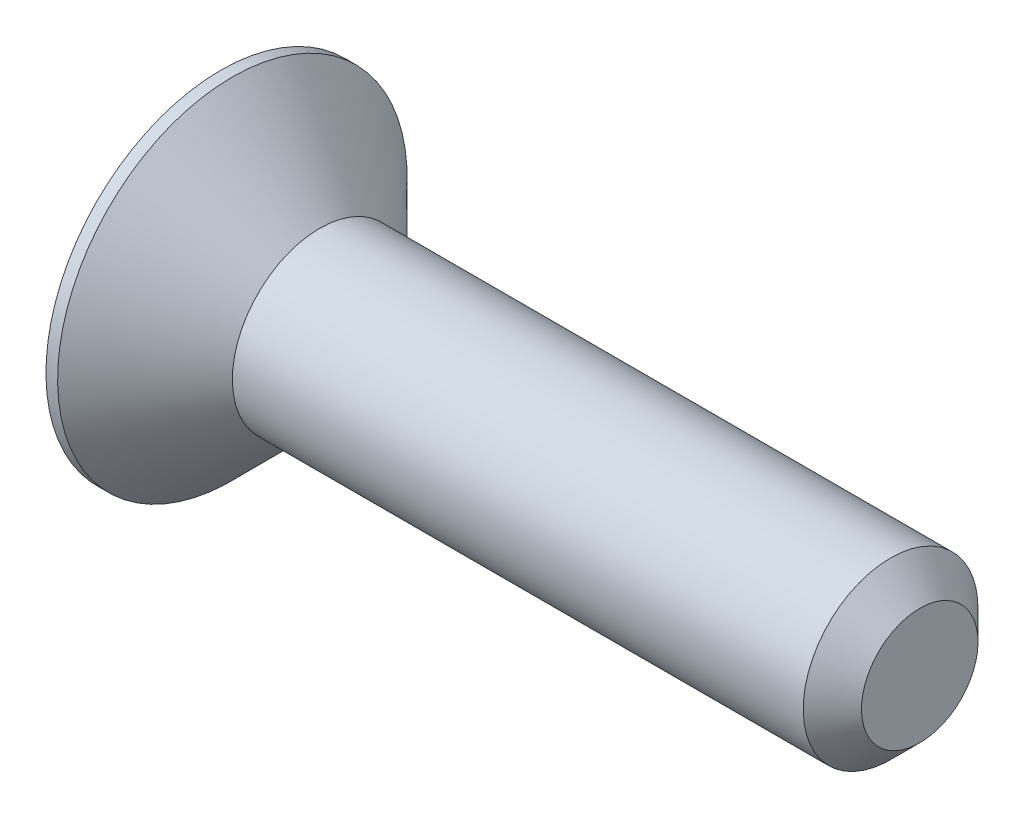
SolidWorks part; units mm, degrees
ref_plane "Plan de face" through (0, 0, 0) normal (0, 0, 1) x (1, 0, 0)
ref_plane "Plan de dessus" through (0, 0, 0) normal (0, 1, 0) x (1, 0, 0)
ref_plane "Plan de droite" through (0, 0, 0) normal (1, 0, 0) x (0, 0, -1)
sketch "Esquisse1" plane through (0, 0, 0) normal (0, 0, 1) x (1, 0, 0)
  line L0 (0, 0) -> (0, 3)
  line L1 (0, 3) -> (0.2, 3)
  line L2 (0.2, 3) -> (1.7, 1.5)
  line L3 (1.7, 1.5) -> (12, 1.5)
  line L4 (12, 1.5) -> (12, 0)
  line L5 (12, 0) -> (0, 0) construction
  line L6 (0, 0) -> (12, 0)
  dimension "D1" = 1.7
  dimension "D2" = 12
  dimension "D3" = 3
  dimension "D4" = 6
  dimension "D5" = 45
revolve "Révolution1" add sketch "Esquisse1" angle 360 about L5
chamfer "Chanfrein1" distance 0.5 angle 45 1 edges at (12, 1.5, 0)
sketch "Esquisse2" plane through (0, 0, 0) normal (-1, 0, 0) x (0, 0, 1)
  line L1 (0, 1.1547) -> (-1, 0.5774)
  line L2 (-1, 0.5774) -> (-1, -0.5774)
  line L3 (-1, -0.5774) -> (0, -1.1547)
  line L4 (0, -1.1547) -> (1, -0.5774)
  line L5 (1, -0.5774) -> (1, 0.5774)
  line L6 (1, 0.5774) -> (0, 1.1547)
  circle A0 centre (0, 0) radius 1 construction
  dimension "D1" = 2
extrude "Enlèv. mat.-Extru.1" cut sketch "Esquisse2" against normal blind 1.2
